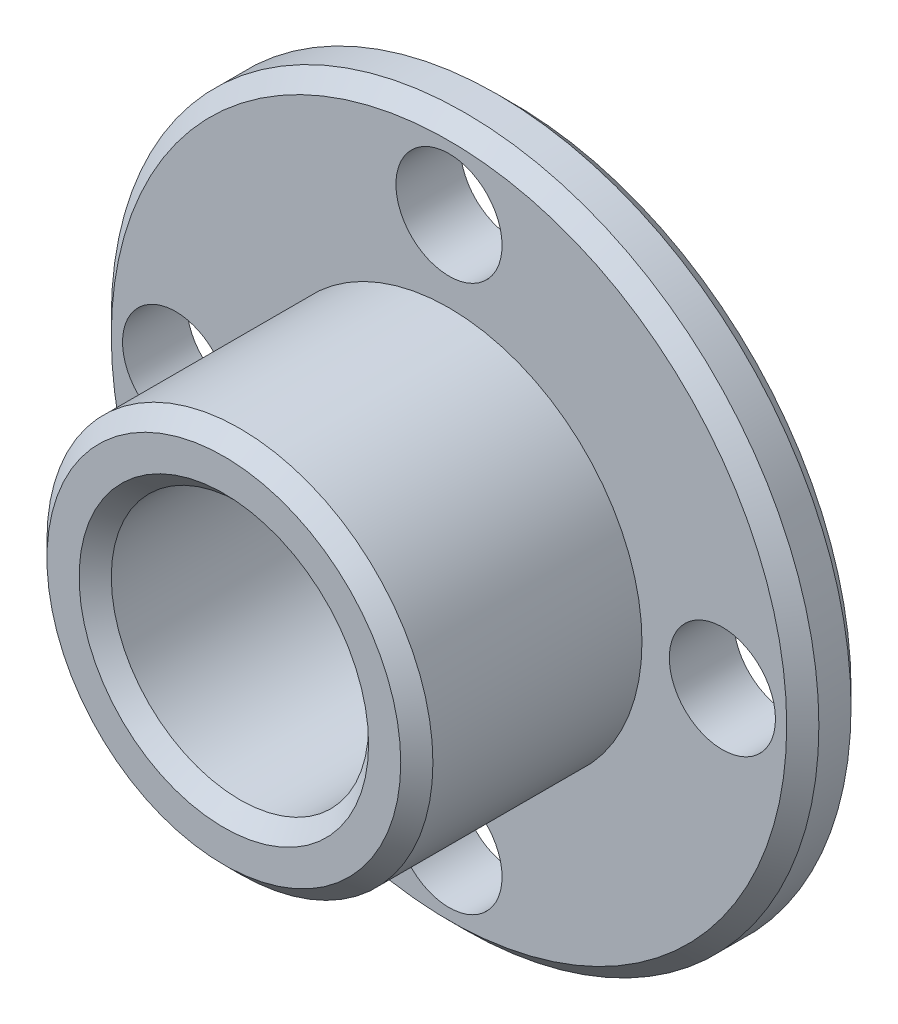
SolidWorks part; units mm, degrees
ref_plane "Face" through (0, 0, 0) normal (0, 0, 1) x (1, 0, 0)
ref_plane "Dessus" through (0, 0, 0) normal (0, 1, 0) x (1, 0, 0)
ref_plane "Droite" through (0, 0, 0) normal (1, 0, 0) x (0, 0, -1)
sketch "Esquisse1" plane through (0, 0, 0) normal (0, 0, 1) x (1, 0, 0)
  line L0 (71.6679, 39.5358) -> (76.6679, 39.5358) construction
  line L1 (65.6679, 48.0358) -> (74.1679, 39.5358) construction
  circle A0 centre (65.6679, 39.5358) radius 4
  circle A1 centre (65.6679, 39.5358) radius 11
  circle A2 centre (65.6679, 39.5358) radius 8.5 construction
  circle A3 centre (65.6679, 48.0358) radius 1.65
  circle A4 centre (65.6679, 39.5358) radius 4 construction
  circle A5 centre (74.1679, 39.5358) radius 1.65
  circle A7 centre (65.6679, 39.5358) radius 4 construction
  circle A8 centre (65.6679, 31.0358) radius 1.65
  circle A9 centre (57.1679, 39.5358) radius 1.65
  circle A10 centre (65.6679, 39.5358) radius 6 construction
  point P8 (74.1679, 39.5358)
  point P20 (65.6679, 39.5358)
  dimension "D1" = 7
  dimension "D2" = 3.3
  dimension "D4" = 2
  dimension "D3" = 4
extrude "Boss.-Extru.1" add sketch "Esquisse1" along normal blind 2
sketch "Esquisse2" plane through (0, 0, 2) normal (0, 0, 1) x (1, 0, 0)
  circle A0 centre (65.6679, 39.5358) radius 6
  circle A1 centre (65.6679, 39.5358) radius 4 construction
  circle A2 centre (65.6679, 39.5358) radius 4
  point P6 (0, 0)
  point P7 (0, 0)
  dimension "D1" = 2
extrude "Boss.-Extru.2" add sketch "Esquisse2" along normal blind 7
chamfer "Chanfrein1" distance 0.5 angle 45 4 edges at (71.6679, 39.5358, 9) (69.6679, 39.5358, 9) (76.6679, 39.5358, 2) (76.6679, 39.5358, 0)
